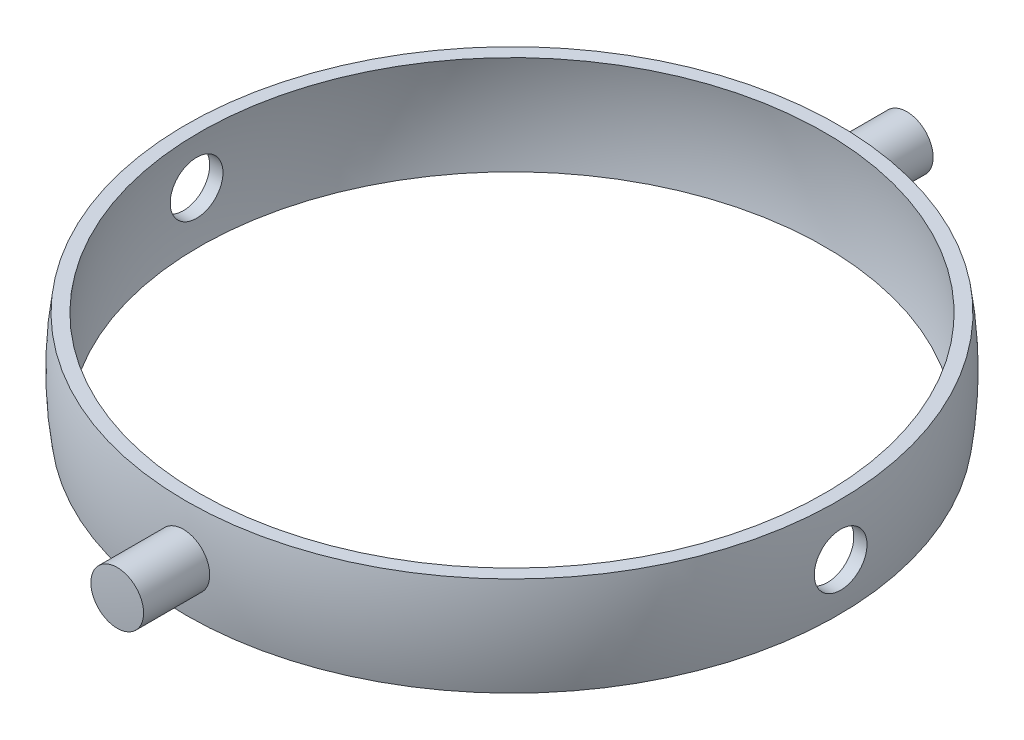
SolidWorks part; units mm, degrees
ref_plane "Front Plane" through (0, 0, 0) normal (0, 0, 1) x (1, 0, 0)
ref_plane "Top Plane" through (0, 0, 0) normal (0, 1, 0) x (1, 0, 0)
ref_plane "Right Plane" through (0, 0, 0) normal (1, 0, 0) x (0, 0, -1)
sketch "Sketch1" plane through (0, 0, 0) normal (0, 0, 1) x (1, 0, 0)
  line L0 (0, 31.2039) -> (0, 0) construction
  line L1 (0, 0) -> (-54.0143, 0) construction
  line L2 (-49.4343, 7.5) -> (-47.4104, 7.5)
  line L3 (-49.4343, -7.5) -> (-47.4104, -7.5)
  arc A0 (-49.4343, 7.5) -> (-49.4343, -7.5) centre (0, 0) ccw
  arc A1 (-47.4104, 7.5) -> (-47.4104, -7.5) centre (0, 0) ccw
  point P8 (-48.4224, -7.5)
  dimension "D1" = 50
  dimension "D2" = 48
  dimension "D3" = 15
revolve "Revolve1" add sketch "Sketch1" angle 360 about L0
sketch "Sketch2" plane through (0, 0, 0) normal (1, 0, 0) x (0, 0, -1)
  line L0 (0, 7.5) -> (0, 0) construction
  line L1 (49.4343, 7.5) -> (-49.4343, 7.5) construction
  circle A0 centre (0, 0) radius 4
  dimension "D1" = 8
  dimension "D2" = 7.5
extrude "Cut-Extrude1" cut sketch "Sketch2" against normal through all both and the other way through all
ref_plane "Plane1" through (0, 0, 60) normal (0, 0, 1) x (1, 0, 0)
sketch "Sketch6" plane through (0, 0, 60) normal (0, 0, 1) x (1, 0, 0)
  circle A0 centre (0, 0) radius 4
  dimension "D1" = 8
extrude "Boss-Extrude1" add sketch "Sketch6" against normal up to surface (10.1603 mm away)
mirror "Mirror1" about plane through (0, 0, 0) normal (0, 0, 1) of "Boss-Extrude1"
sketch "Sketch8" plane through (0, 0, 0) normal (1, 0, 0) x (0, 0, -1)
  line L0 (0, 45.192) -> (0, 0) construction
  line L1 (0, 0) -> (-60.7679, 0) construction
  line L2 (0, 70) -> (0, 60)
  line L3 (0, -60) -> (0, -70)
  arc A1 (0, 60) -> (0, -60) centre (0, 0) ccw
  arc A2 (0, -70) -> (0, 70) centre (0, 0) cw
  point P8 (0, 0)
  point P9 (0, 0)
  point P10 (0, 0)
  dimension "D1" = 60
  dimension "D2" = 70
revolve "Cut-Revolve1" cut sketch "Sketch8" angle 360 about L0
